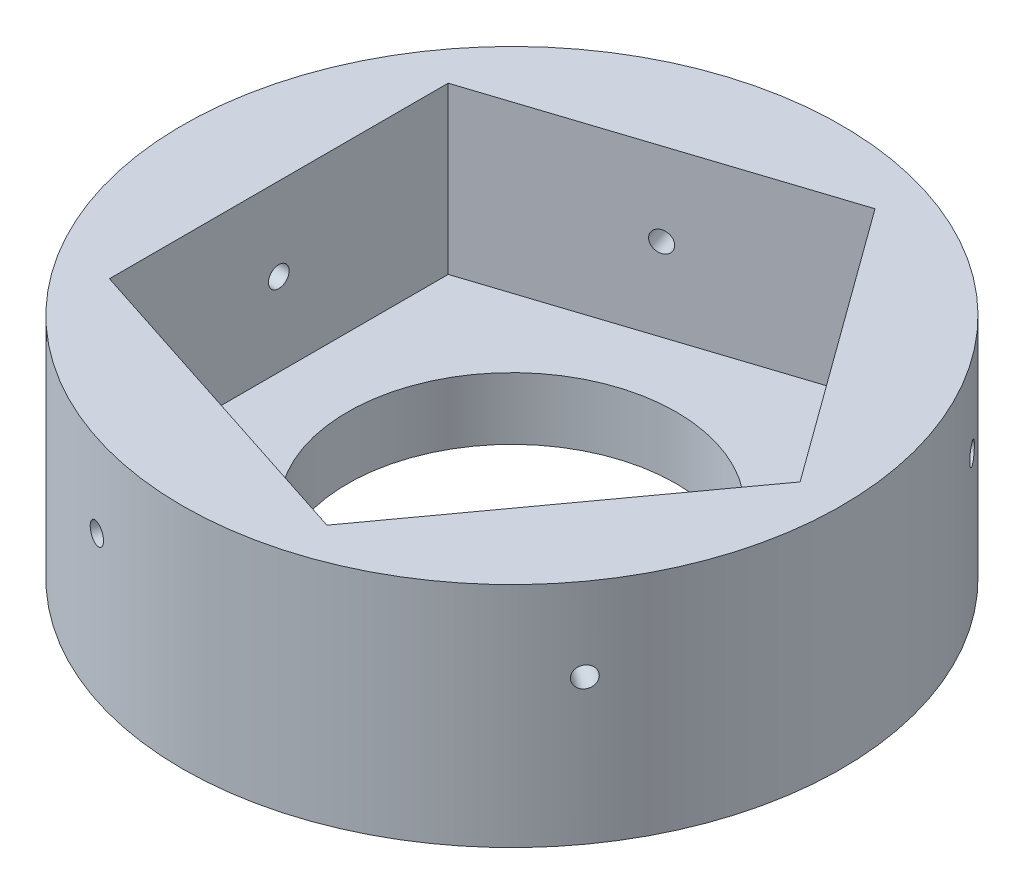
SolidWorks part; units mm, degrees
material "ABS"
ref_plane "Front Plane" through (0, 0, 0) normal (0, 0, 1) x (1, 0, 0)
ref_plane "Top Plane" through (0, 0, 0) normal (0, 1, 0) x (1, 0, 0)
ref_plane "Right Plane" through (0, 0, 0) normal (1, 0, 0) x (0, 0, -1)
sketch "Sketch1" plane through (0, 0, 0) normal (0, 1, 0) x (1, 0, 0)
  line L1 (69.5798, 0) -> (21.5014, 66.1744) construction
  line L2 (21.5014, 66.1744) -> (-56.2913, 40.898) construction
  line L3 (-56.2913, 40.898) -> (-56.2913, -40.898) construction
  line L4 (-56.2913, -40.898) -> (21.5014, -66.1744) construction
  line L5 (21.5014, -66.1744) -> (69.5798, 0) construction
  circle A1 centre (0, 0) radius 39.6875
  circle A2 centre (0, 0) radius 69.5798
  dimension "D1" = 79.375
  dimension "D2" = 81.796
extrude "Boss-Extrude1" add sketch "Sketch1" along normal blind 15
sketch "Sketch2" plane through (0, 15, 0) normal (0, 1, 0) x (1, 0, 0)
  circle A0 centre (0, 0) radius 69.5798 construction
  circle A4 centre (0, 0) radius 79.5798
  circle A5 centre (0, 0) radius 69.5798
  dimension "D1" = 10
extrude "Boss-Extrude2" add sketch "Sketch2" along normal blind 40 and the other way up to surface (15 mm away) other way up to face at (0, 0, 69.5798)
sketch "Sketch3" plane through (0, 15, 0) normal (0, 1, 0) x (1, 0, 0)
  line L1 (69.5798, 0) -> (21.5014, 66.1744)
  line L2 (21.5014, 66.1744) -> (-56.2913, 40.898)
  line L3 (-56.2913, 40.898) -> (-56.2913, -40.898)
  line L4 (-56.2913, -40.898) -> (21.5014, -66.1744)
  line L5 (21.5014, -66.1744) -> (69.5798, 0)
  circle A0 centre (0, 0) radius 69.5798 construction
  circle A1 centre (0, 0) radius 69.5798 construction
extrude "Boss-Extrude3" add sketch "Sketch3" along normal up to surface (40 mm away)
sketch "Sketch4" plane through (-17.395, 0, -53.5362) normal (0.309, 0, 0.9511) x (0.9511, 0, -0.309)
  line L1 (-40.898, 55) -> (-40.898, 15) construction
  line L2 (40.898, 55) -> (-40.898, 55) construction
  circle A0 centre (0, 35) radius 2.5
  point P5 (-40.898, 35)
  point P11 (0, 55)
  dimension "D1" = 5
extrude "Cut-Extrude1" cut sketch "Sketch4" against normal through all
pattern_circular "CirPattern1" count 5 over 360 about axis through (0, -225.0858, 0) along (0, 1, 0) of "Cut-Extrude1"
equation "\"Rope\"= 5in / 8"
equation "\"D1@Sketch1\"=\"Rope\"*5"
